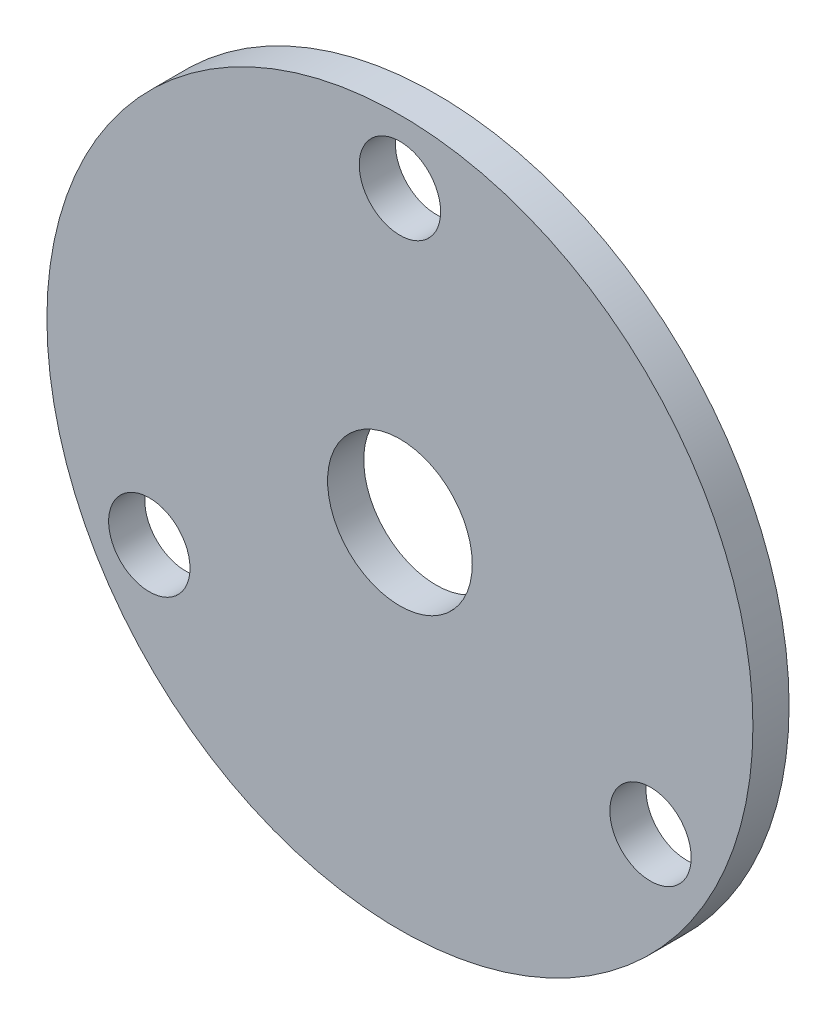
SolidWorks part; units mm, degrees
material "6061-T6 Al"
ref_plane "Front" through (0, 0, 0) normal (0, 0, 1) x (1, 0, 0)
ref_plane "Top" through (0, 0, 0) normal (0, 1, 0) x (1, 0, 0)
ref_plane "Right" through (0, 0, 0) normal (1, 0, 0) x (0, 0, -1)
sketch "Sketch1" plane through (0, 0, 0) normal (0, 0, 1) x (1, 0, 0)
  circle A0 centre (0, 0) radius 61.976
  dimension "D1" = 123.952
extrude "Boss-Extrude1" add sketch "Sketch1" along normal blind 6.35
hole_wizard "1 (1) Diameter Hole1" positions "Sketch3" profile "Sketch4" hole size "1" standard "Ansi Inch" end condition through all
sketch "Sketch3" plane through (0, 0, 6.35) normal (0, 0, 1) x (1, 0, 0)
  point P0 (0, 0)
sketch "Sketch4" plane through (0, 0, 6.35) normal (1, 0, 0) x (0, -1, 0)
  line L0 (0, 0) -> (0, 6.35)
  line L1 (0, 6.35) -> (12.7, 6.35)
  line L2 (12.7, 6.35) -> (12.7, 0)
  line L5 (12.7, 0) -> (0, 0)
  line L11 (0, -6.35) -> (0, 107.95) construction
  dimension "Thru Hole Dia." = 25.4
  dimension "Thru Hole Depth" = 6.35
hole_wizard "9/16 (0.5625) Diameter Hole1" positions "Sketch6" profile "Sketch7" hole size "9/16" standard "Ansi Inch" end condition through all
sketch "Sketch6" plane through (0, 0, 6.35) normal (0, 0, 1) x (1, 0, 0)
  line L0 (0, 0) -> (0, 50.8) construction
  line L1 (-43.9941, -25.4) -> (0, 0) construction
  line L2 (0, 0) -> (43.9941, -25.4) construction
  circle A0 centre (0, 0) radius 50.8
  point P0 (-43.9941, -25.4)
  point P1 (43.9941, -25.4)
  point P3 (0, 50.8)
  dimension "D1" = 50.8
  dimension "D2" = 120
  dimension "D3" = 120
sketch "Sketch7" plane through (-43.9941, -25.4, 6.35) normal (1, 0, 0) x (0, -1, 0)
  line L0 (0, 0) -> (0, 6.35)
  line L1 (0, 6.35) -> (7.1437, 6.35)
  line L2 (7.1437, 6.35) -> (7.1437, 0)
  line L5 (7.1437, 0) -> (0, 0)
  line L11 (0, -6.35) -> (0, 107.95) construction
  dimension "Thru Hole Dia." = 14.2875
  dimension "Thru Hole Depth" = 6.35
